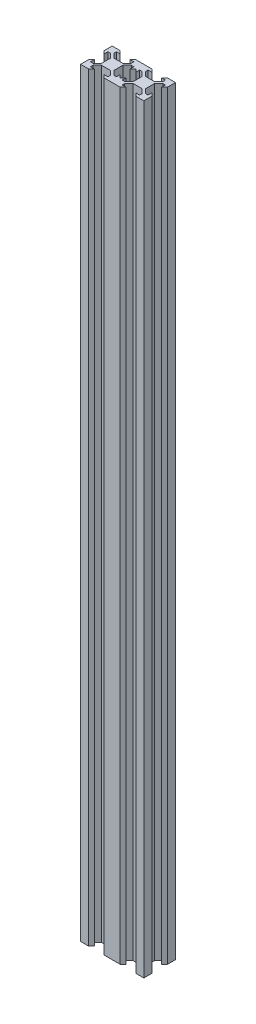
SolidWorks part; units mm, degrees
ref_plane "Front Plane" through (0, 0, 0) normal (0, 0, 1) x (1, 0, 0)
ref_plane "Top Plane" through (0, 0, 0) normal (0, 1, 0) x (1, 0, 0)
ref_plane "Right Plane" through (0, 0, 0) normal (1, 0, 0) x (0, 0, -1)
sketch "Sketch1" plane through (0, 0, 0) normal (0, 1, 0) x (1, 0, 0)
  line L0 (0, 93.8825) -> (0, -83.9719) construction
  line L1 (2.84, -3.9007) -> (-2.84, -3.9007)
  line L2 (3.9007, -2.84) -> (3.9007, 2.84)
  line L3 (2.84, 3.9007) -> (-2.84, 3.9007)
  line L4 (-3.9007, -2.84) -> (-3.9007, 2.84)
  line L7 (-194.997, 0) -> (154.5512, 0) construction
  line L8 (-2.84, -3.9007) -> (-5.4993, -6.56)
  line L9 (-5.4993, -6.56) -> (-5.4993, -8.2)
  line L10 (-5.4993, -8.2) -> (-3.1, -8.2)
  line L11 (-3.1, -8.2) -> (-4.9, -10)
  line L12 (-4.9, -10) -> (-10, -10)
  line L13 (-3.9007, -2.84) -> (-6.56, -5.4993)
  line L14 (-6.56, -5.4993) -> (-8.2, -5.4993)
  line L15 (-8.2, -5.4993) -> (-8.2, -3.1)
  line L16 (-8.2, -3.1) -> (-10, -4.9)
  line L17 (-10, -4.9) -> (-10, -10)
  line L18 (10, -4.9) -> (10, -10)
  line L19 (8.2, -3.1) -> (10, -4.9)
  line L20 (8.2, -5.4993) -> (8.2, -3.1)
  line L21 (6.56, -5.4993) -> (8.2, -5.4993)
  line L22 (3.9007, -2.84) -> (6.56, -5.4993)
  line L23 (4.9, -10) -> (10, -10)
  line L24 (3.1, -8.2) -> (4.9, -10)
  line L25 (5.4993, -8.2) -> (3.1, -8.2)
  line L26 (5.4993, -6.56) -> (5.4993, -8.2)
  line L27 (2.84, -3.9007) -> (5.4993, -6.56)
  line L28 (2.84, 3.9007) -> (5.4993, 6.56)
  line L29 (5.4993, 6.56) -> (5.4993, 8.2)
  line L30 (5.4993, 8.2) -> (3.1, 8.2)
  line L31 (3.1, 8.2) -> (4.9, 10)
  line L32 (4.9, 10) -> (10, 10)
  line L33 (3.9007, 2.84) -> (6.56, 5.4993)
  line L34 (6.56, 5.4993) -> (8.2, 5.4993)
  line L35 (8.2, 5.4993) -> (8.2, 3.1)
  line L36 (8.2, 3.1) -> (10, 4.9)
  line L37 (10, 4.9) -> (10, 10)
  line L38 (-10, 4.9) -> (-10, 10)
  line L39 (-8.2, 3.1) -> (-10, 4.9)
  line L40 (-8.2, 5.4993) -> (-8.2, 3.1)
  line L41 (-6.56, 5.4993) -> (-8.2, 5.4993)
  line L42 (-3.9007, 2.84) -> (-6.56, 5.4993)
  line L43 (-4.9, 10) -> (-10, 10)
  line L44 (-3.1, 8.2) -> (-4.9, 10)
  line L45 (-5.4993, 8.2) -> (-3.1, 8.2)
  line L46 (-5.4993, 6.56) -> (-5.4993, 8.2)
  line L47 (-2.84, 3.9007) -> (-5.4993, 6.56)
  point P0 (0, 0)
  point P4 (4.1697, 5.2303)
  dimension "D1" = 90
  dimension "D2" = 20
  dimension "D3" = 1.64
  dimension "D4" = 1.5
  dimension "D5" = 6.2
  dimension "D6" = 5.68
  dimension "D7" = 1.8
extrude "Boss-Extrude1" add sketch "Sketch1" along normal blind 480
pattern_linear "LPattern1" count 2 spacing 20 along (1, 0, 0) of "Boss-Extrude1"
